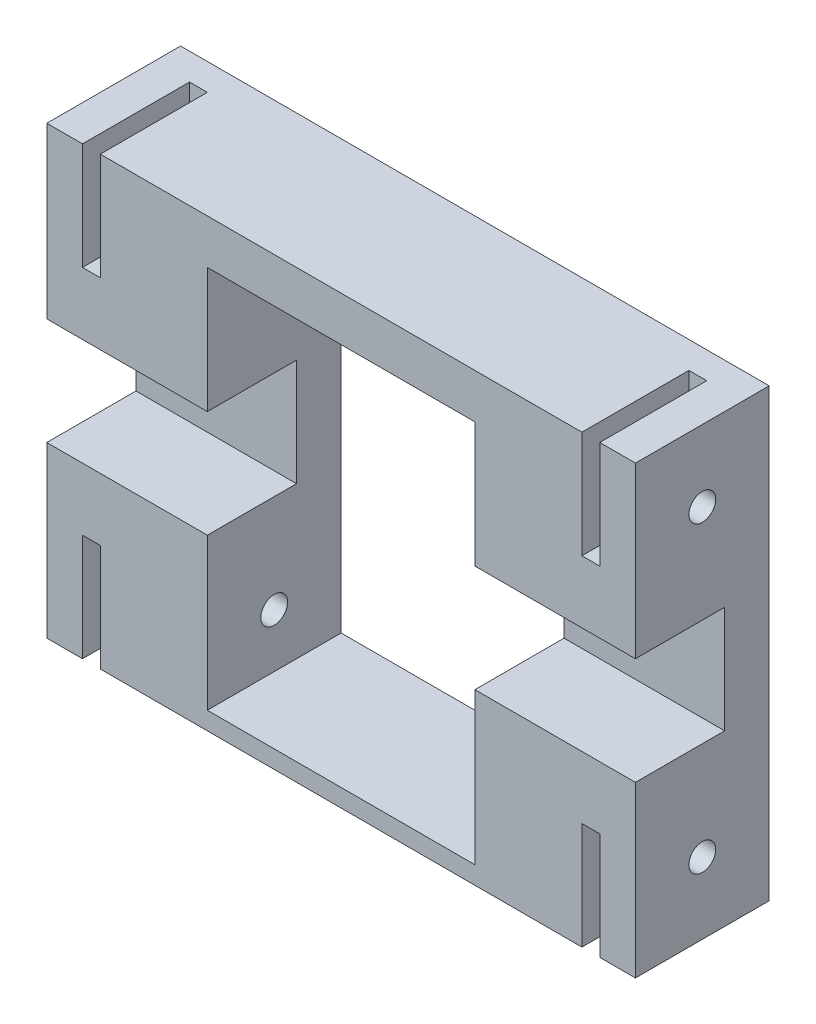
SolidWorks part; units mm, degrees
ref_plane "Alzado" through (0, 0, 0) normal (0, 0, 1) x (1, 0, 0)
ref_plane "Planta" through (0, 0, 0) normal (0, 1, 0) x (1, 0, 0)
ref_plane "Vista lateral" through (0, 0, 0) normal (1, 0, 0) x (0, 0, -1)
sketch "Croquis1" plane through (0, 0, 0) normal (0, 0, 1) x (1, 0, 0)
  line L1 (0, 0) -> (66, 0)
  line L2 (0, 0) -> (0, 50)
  line L3 (0, 50) -> (66, 50)
  line L4 (66, 0) -> (66, 50)
  line L5 (18, 2) -> (48, 2)
  line L6 (18, 2) -> (18, 45)
  line L7 (18, 45) -> (48, 45)
  line L8 (48, 2) -> (48, 45)
  dimension "D1" = 66
  dimension "D2" = 50
  dimension "D3" = 18
  dimension "D4" = 18
  dimension "D5" = 5
  dimension "D6" = 2
extrude "Saliente-Extruir1" add sketch "Croquis1" along normal blind 15
sketch "Croquis2" plane through (0, 0, 0) normal (-1, 0, 0) x (0, 0, 1)
  line L0 (15, 25) -> (0, 25) construction
  line L1 (15, 50) -> (15, 0) construction
  line L2 (0, 50) -> (0, 0) construction
  line L3 (15, 19) -> (15, 31)
  line L4 (15, 31) -> (5, 31)
  line L5 (5, 31) -> (5, 19)
  line L6 (15, 19) -> (5, 19)
  circle A0 centre (7.5, 42) radius 1.5
  circle A1 centre (7.5, 8) radius 1.5
  point P14 (5, 25)
  dimension "D3" = 3
  dimension "D1" = 6
  dimension "D2" = 10
  dimension "D4" = 17
  dimension "D5" = 7.5
extrude "Cortar-Extruir1" cut sketch "Croquis2" against normal through all
sketch "Croquis3" plane through (0, 0, 15) normal (0, 0, 1) x (1, 0, 0)
  line L0 (66, 50) -> (0, 50) construction
  line L1 (4, 50) -> (6, 50)
  line L2 (4, 50) -> (4, 38)
  line L3 (4, 38) -> (6, 38)
  line L4 (6, 50) -> (6, 38)
  line L5 (0, 0) -> (0, 50) construction
  line L6 (0, 25) -> (66.3794, 25) construction
  line L7 (33, 50) -> (33, 0) construction
  line L8 (0, 0) -> (66, 0) construction
  line L9 (60, 50) -> (60, 38)
  line L10 (62, 38) -> (60, 38)
  line L11 (62, 50) -> (62, 38)
  line L12 (62, 50) -> (60, 50)
  line L13 (4, 12) -> (6, 12)
  line L14 (62, 0) -> (60, 0)
  line L15 (62, 0) -> (62, 12)
  line L16 (62, 12) -> (60, 12)
  line L17 (60, 0) -> (60, 12)
  line L18 (6, 0) -> (6, 12)
  line L19 (4, 0) -> (4, 12)
  line L20 (4, 0) -> (6, 0)
  dimension "D1" = 2
  dimension "D2" = 12
  dimension "D3" = 4
extrude "Cortar-Extruir2" cut sketch "Croquis3" against normal blind 12
